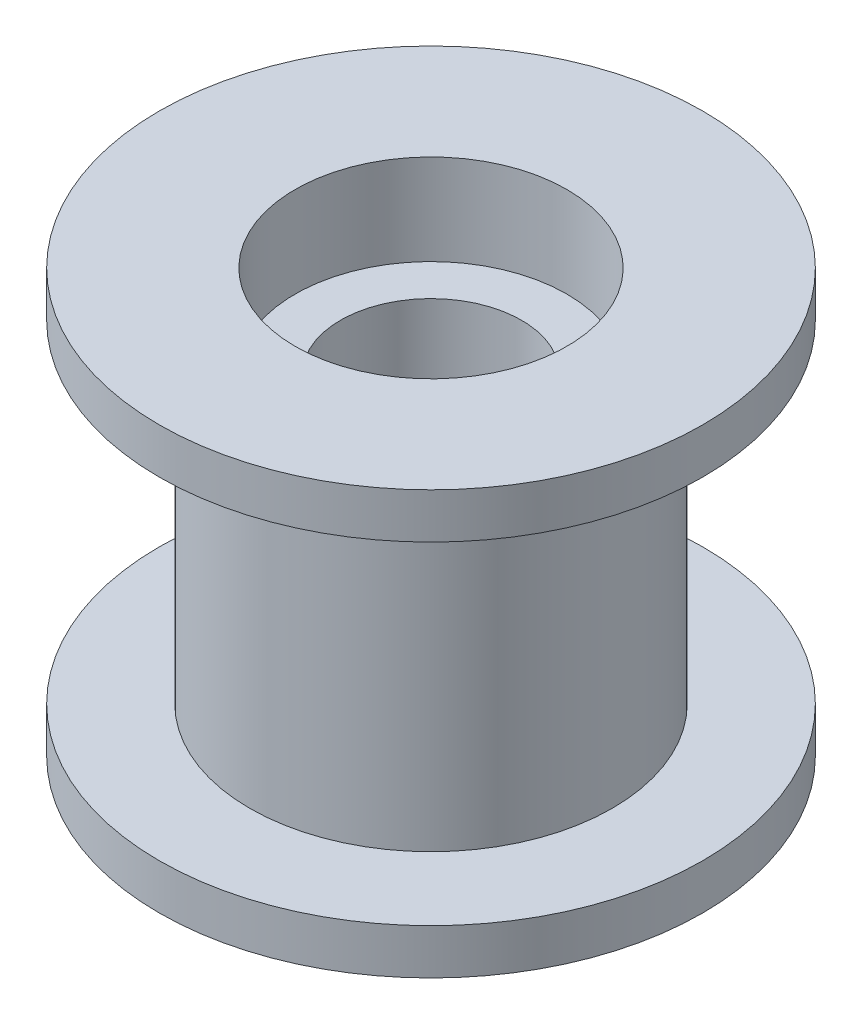
SolidWorks part; units mm, degrees
material "6061 Alloy"
ref_plane "Front Plane" through (0, 0, 0) normal (0, 0, 1) x (1, 0, 0)
ref_plane "Top Plane" through (0, 0, 0) normal (0, 1, 0) x (1, 0, 0)
ref_plane "Right Plane" through (0, 0, 0) normal (1, 0, 0) x (0, 0, -1)
sketch "Sketch1" plane through (0, 0, 0) normal (0, 1, 0) x (1, 0, 0)
  circle A0 centre (0, 0) radius 6
  circle A1 centre (0, 0) radius 4.5
  dimension "D1" = 9
  dimension "D2" = 12
extrude "Boss-Extrude1" add sketch "Sketch1" along normal mid plane 11
sketch "Sketch2" plane through (0, 5.5, 0) normal (0, 1, 0) x (1, 0, 0)
  circle A0 centre (0, 0) radius 9
  circle A1 centre (0, 0) radius 4.5
  circle A2 centre (0, 0) radius 4.5 construction
  dimension "D1" = 18
extrude "Boss-Extrude2" add sketch "Sketch2" along normal blind 1.5
mirror "Mirror1" about plane through (0, 0, 0) normal (0, 1, 0) of "Boss-Extrude2"
sketch "Sketch3" plane through (0, 0, 0) normal (0, 1, 0) x (1, 0, 0)
  circle A0 centre (0, 0) radius 4.5
  circle A1 centre (0, 0) radius 4.5 construction
  circle A2 centre (0, 0) radius 3
  dimension "D1" = 6
extrude "Boss-Extrude3" add sketch "Sketch3" along normal mid plane 8
